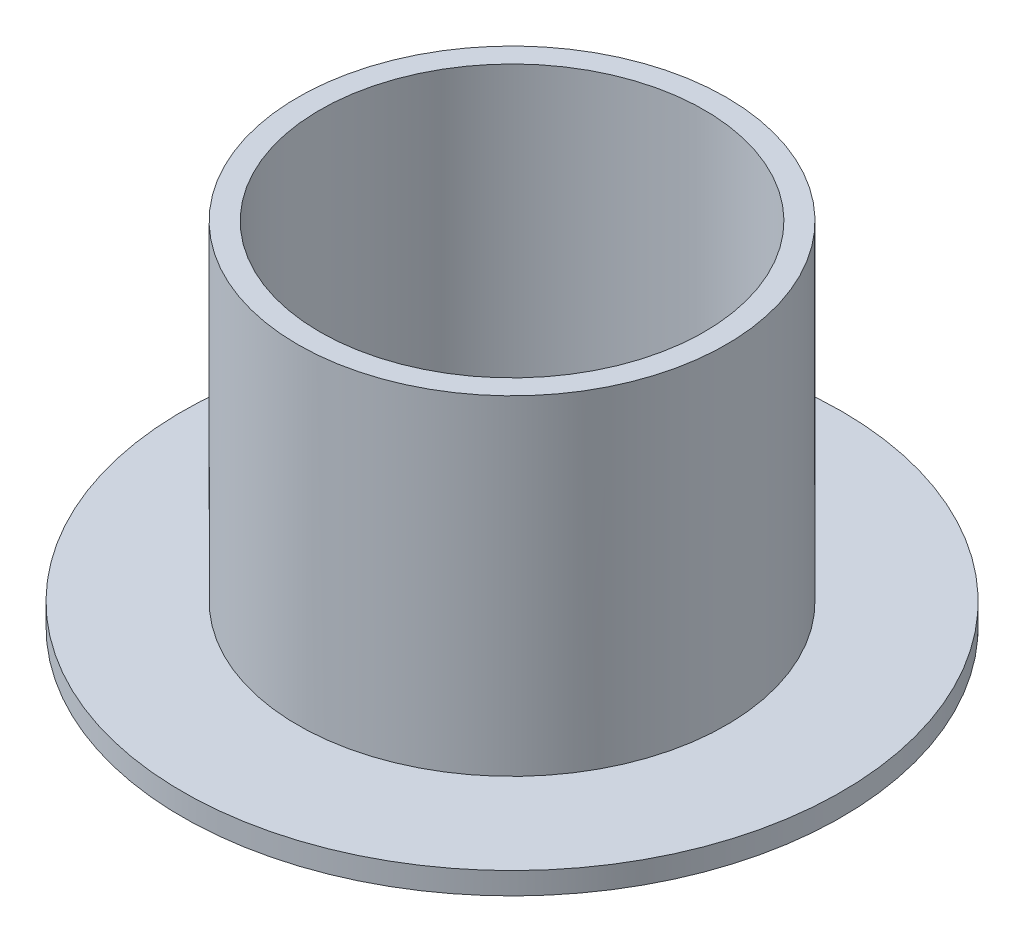
SolidWorks part; units mm, degrees
ref_plane "Front Plane" through (0, 0, 0) normal (0, 0, 1) x (1, 0, 0)
ref_plane "Top Plane" through (0, 0, 0) normal (0, 1, 0) x (1, 0, 0)
ref_plane "Right Plane" through (0, 0, 0) normal (1, 0, 0) x (0, 0, -1)
sketch "Sketch1" plane through (0, 0, 0) normal (0, 1, 0) x (1, 0, 0)
  circle A0 centre (0, 0) radius 17.5
  circle A1 centre (0, 0) radius 19.5
  dimension "D1" = 35
  dimension "D2" = 2
extrude "Boss-Extrude1" add sketch "Sketch1" along normal blind 30
sketch "Sketch2" plane through (0, 0, 0) normal (0, -1, 0) x (1, 0, 0)
  circle A0 centre (0, 0) radius 30
  dimension "D1" = 60
extrude "Boss-Extrude2" add sketch "Sketch2" along normal blind 2
